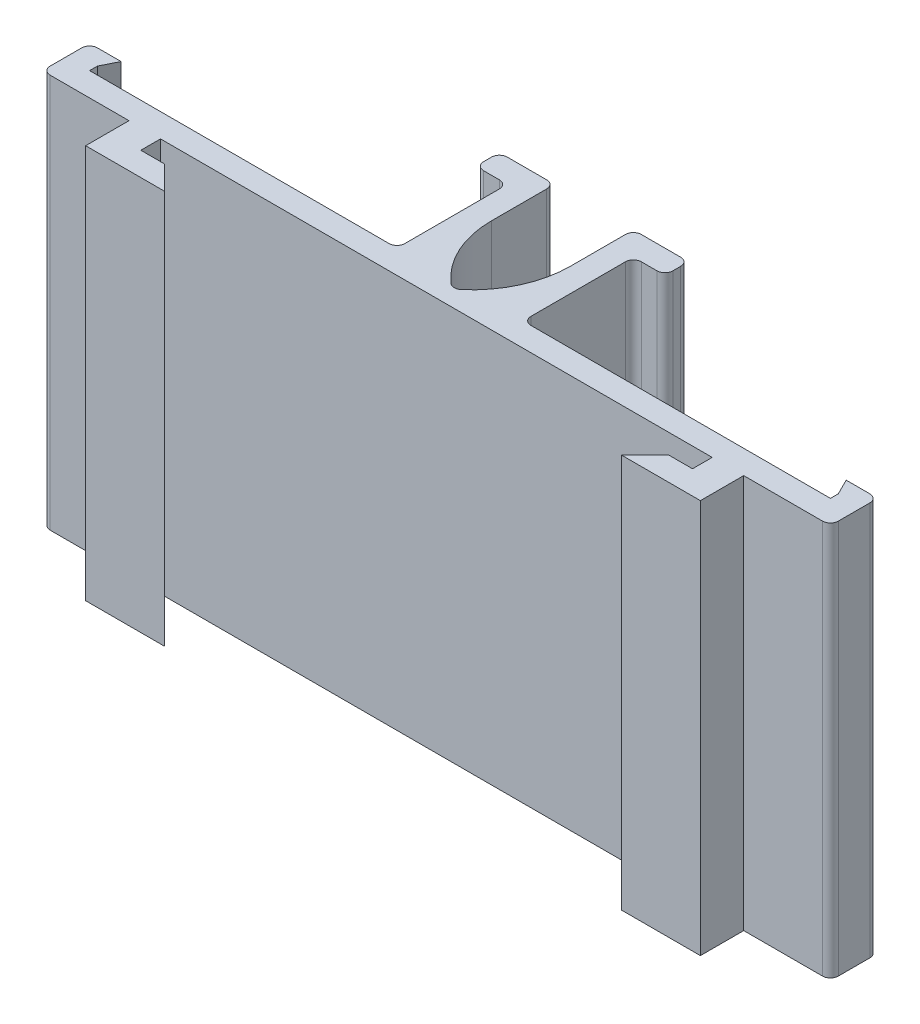
SolidWorks part; units mm, degrees
ref_plane "Front Plane" through (0, 0, 0) normal (0, 0, 1) x (1, 0, 0)
ref_plane "Top Plane" through (0, 0, 0) normal (0, 1, 0) x (1, 0, 0)
ref_plane "Right Plane" through (0, 0, 0) normal (1, 0, 0) x (0, 0, -1)
sketch "Sketch6" plane through (0, 0, 0) normal (0, 1, 0) x (1, 0, 0)
  line L1 (-23.5, 1.5) -> (-4, 1.5)
  line L2 (-23.5, 1.5) -> (-23.5, 2)
  line L3 (-6, 8.5) -> (-4, 8.5)
  line L4 (-4, 1.5) -> (-4, 8.5)
  line L8 (0, -6.05) -> (0, 6.05) construction
  line L13 (-2.5, 6) -> (-2.5, 10)
  line L14 (-6, 10) -> (-2.5, 10)
  line L15 (-25, 0) -> (-25, 3)
  line L16 (-25, 0) -> (-2.5, 0)
  line L17 (6, 10) -> (6, 8.5)
  line L18 (-23.5, 2) -> (-23, 3)
  line L19 (-23, 3) -> (-25, 3)
  line L20 (-25, 10) -> (-2.5, 10) construction
  line L21 (-23.5, 1.5) -> (-23.5, 8.5) construction
  line L22 (-25, 0) -> (-25, 10) construction
  line L23 (-6, 10) -> (-6, 8.5)
  line L24 (23, 3) -> (25, 3)
  line L25 (-23.5, 8.5) -> (-4, 8.5) construction
  line L26 (23.5, 2) -> (23, 3)
  line L27 (25, 0) -> (2.5, 0)
  line L28 (25, 0) -> (25, 3)
  line L29 (6, 10) -> (2.5, 10)
  line L30 (2.5, 6) -> (2.5, 10)
  line L31 (4, 1.5) -> (4, 8.5)
  line L32 (6, 8.5) -> (4, 8.5)
  line L33 (23.5, 1.5) -> (23.5, 2)
  line L34 (23.5, 1.5) -> (4, 1.5)
  line L35 (-2.5, 0) -> (2.5, 0) construction
  line L38 (-2.5, 0) -> (2.5, 0)
  line L39 (-2.5, 0) -> (-2.5, 10) construction
  arc A0 (-2.5, 6) -> (0, 1) centre (3.75, 6) ccw
  arc A1 (2.5, 6) -> (0, 1) centre (-3.75, 6) cw
  point P5 (0, 0)
  dimension "D1" = 7
  dimension "D2" = 19.5
  dimension "D3" = 1.5
  dimension "D4" = 0.5
  dimension "D5" = 3
  dimension "D6" = 2
  dimension "D7" = 2
  dimension "D8" = 5
  dimension "D9" = 5
  dimension "D10" = 1
extrude "Boss-Extrude1" add sketch "Sketch6" along normal blind 25
fillet "Fillet1" radius 0.5 5 edges at (0, 12.5, -1) (4, 12.5, -8.5) (-4, 12.5, -8.5) (4, 12.5, -1.5) (-4, 12.5, -1.5)
fillet "Fillet2" radius 0.5 10 edges at (25, 12.5, -3) (25, 12.5, 0) (-25, 12.5, 0) (-25, 12.5, -3) (6, 12.5, -8.5) (6, 12.5, -10) (2.5, 12.5, -10) (-2.5, 12.5, -10) (-6, 12.5, -8.5) (-6, 12.5, -10)
sketch "Sketch7" plane through (0, 25, 0) normal (0, 1, 0) x (1, 0, 0)
  line L0 (-19.5, 0) -> (-19.5, -2.75)
  line L1 (-24.5, 0) -> (24.5, 0) construction
  line L2 (-19.5, -2.75) -> (-14.5, -2.75)
  line L3 (-14.5, -2.75) -> (-16, -1.25)
  line L4 (-16, -1.25) -> (-17.5, -1.25)
  line L5 (-17.5, -1.25) -> (-17.5, 0)
  line L6 (-19.5, 0) -> (-17.5, 0)
  line L7 (0, -5.5) -> (0, 5.5) construction
  line L8 (19.5, 0) -> (17.5, 0)
  line L9 (17.5, -1.25) -> (17.5, 0)
  line L10 (16, -1.25) -> (17.5, -1.25)
  line L11 (14.5, -2.75) -> (16, -1.25)
  line L12 (19.5, -2.75) -> (14.5, -2.75)
  line L13 (19.5, 0) -> (19.5, -2.75)
  dimension "D1" = 1.25
  dimension "D2" = 1.5
  dimension "D3" = 35
  dimension "D4" = 2
  dimension "D5" = 45
  dimension "D6" = 1.5
extrude "Boss-Extrude2" add sketch "Sketch7" against normal up to surface (25 mm away) up to face at (0, 0, -5.0562)
